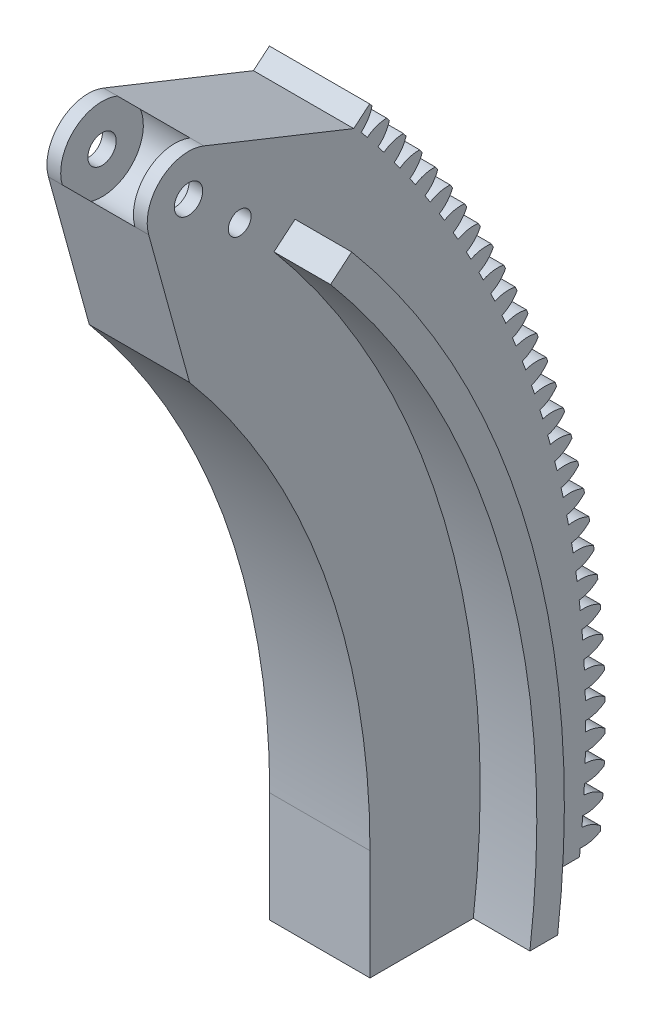
SolidWorks part; units mm, degrees
material "ABS"
ref_plane "Front Plane" through (0, 0, 0) normal (0, 0, 1) x (1, 0, 0)
ref_plane "Top Plane" through (0, 0, 0) normal (0, 1, 0) x (1, 0, 0)
ref_plane "Right Plane" through (0, 0, 0) normal (1, 0, 0) x (0, 0, -1)
ref_plane "idk" through (6.35, 0, 0) normal (1, 0, 0) x (0, 0, -1)
sketch "Sketch1" plane through (0, 0, 0) normal (1, 0, 0) x (0, 0, -1)
  line L0 (-1000, 0) -> (177.8, 0) construction
  line L1 (177.8, 0) -> (177.8, -25.4)
  line L2 (0, 0) -> (136.2027, 114.2876) construction
  line L4 (227.2, 0) -> (49000, 0) construction
  line L7 (177.8, -25.4) -> (227.2, -25.4) construction
  line L8 (227.2, 0) -> (227.2, -25.4) construction
  line L10 (-1.0719, -0.8495) -> (179.1555, 141.9904) construction
  line L61 (181.0098, 139.6187) -> (0, 0) construction
  line L62 (136.2027, 114.2876) -> (126.7844, 148.4774)
  line L64 (177.8, -25.4) -> (225.7757, -25.4)
  line L65 (136.2027, 114.2876) -> (155.124, 130.1645) construction
  line L66 (155.124, 130.1645) -> (174.0453, 146.0413) construction
  line L68 (0, 0) -> (35966.99, 34732.9185) construction
  line L69 (178.0587, 141.1212) -> (178.0836, 141.1409) construction
  line L70 (0, 0) -> (135.9673, 151.007) construction
  line L71 (139.5033, 159.8514) -> (174.0453, 146.0413)
  arc A2 (177.8, 0) -> (136.2027, 114.2876) centre (0, 0) ccw
  circle A19 centre (0, 0) radius 228.6 construction
  arc A22 (174.0453, 146.0413) -> (227.2, 0) centre (0, 0) cw
  arc A23 (227.2, 0) -> (225.7757, -25.4) centre (0, 0) cw
  arc A24 (126.7844, 148.4774) -> (139.5033, 159.8514) centre (135.9673, 151.007) cw
  point P6 (178.0836, 141.1409)
  point P7 (136.2027, 114.2876)
  dimension "D1" = 177.8
  dimension "D2" = 6.35
  dimension "D12" = 457.2
  dimension "D8" = 9.525
  dimension "D3" = 40
  dimension "D4" = 49.4
  dimension "D5" = 25.4
  dimension "D6" = 203.2
  dimension "D7" = 48
  dimension "D13" = 44
sketch "Sketch2" plane through (6.35, 0, 0) normal (1, 0, 0) x (0, 0, -1)
  line L0 (0, 0) -> (165.1, 0) construction
  line L1 (165.1, 0) -> (190.5, 0) construction
  line L2 (0, 0) -> (49240.3877, 8682.4089) construction
  circle A0 centre (165.1, 0) radius 3.2639
  circle A1 centre (190.5, 0) radius 3.2639
  arc A3 (165.1, 0) -> (162.5918, 28.6693) centre (0, 0) ccw construction
  circle A4 centre (162.5918, 28.6693) radius 3.2639
  arc A5 (190.5, 0) -> (187.6059, 33.08) centre (0, 0) ccw construction
  circle A6 centre (187.6059, 33.08) radius 3.2639
  dimension "D3" = 6.5278
  dimension "D4" = 6.5278
  dimension "D6" = 6.5278
  dimension "D7" = 6.5278
  dimension "D1" = 165.1
  dimension "D2" = 25.4
  dimension "D5" = 10
sketch "Sketch11" plane through (6.35, 0, 0) normal (1, 0, 0) x (0, 0, -1)
  line L0 (-785.502, -659.1144) -> (0, 0) construction
  line L2 (-1000, 0) -> (0, 0) construction
  line L4 (155.6602, 130.6144) -> (177.7223, 149.1267)
  line L5 (177.7223, 149.1267) -> (921.7047, 773.4021) construction
  line L6 (232, 0) -> (232, -25.4) construction
  line L7 (232, -25.4) -> (222.9391, -25.4) construction
  line L8 (201.6062, -25.4) -> (230.6054, -25.4)
  line L9 (203.2, 0) -> (232, 0) construction
  arc A0 (-230, 0) -> (-176.1902, -147.8412) centre (0, 0) ccw construction
  arc A1 (-232, 0) -> (-177.7223, -149.1267) centre (0, 0) ccw construction
  arc A2 (-229.6, 0) -> (-175.8838, -147.584) centre (0, 0) ccw construction
  arc A3 (232, 0) -> (177.7223, 149.1267) centre (0, 0) ccw
  arc A4 (230, 0) -> (176.1902, 147.8412) centre (0, 0) ccw construction
  arc A5 (-229.6, 0) -> (-175.8838, -147.584) centre (0, 0) ccw
  arc A6 (155.6602, 130.6144) -> (203.2, 0) centre (0, 0) cw
  arc A7 (232, 0) -> (230.6054, -25.4) centre (0, 0) cw
  arc A8 (203.2, 0) -> (201.6062, -25.4) centre (0, 0) cw
  dimension "D1" = 460
  dimension "D2" = 464
  dimension "D4" = 203.2
  dimension "D3" = 2.4
  dimension "D6" = 25.4
extrude "Teeth blank" add sketch "Sketch11" against normal blind 6.35
sketch "Sketch12" plane through (6.35, 0, 0) normal (1, 0, 0) x (0, 0, -1)
  line L0 (0, 0) -> (232, 0) construction
  line L2 (229.9946, 1.5708) -> (229.9946, -1.5708) construction
  line L3 (0, 0) -> (227.4972, 1.1241) construction
  line L4 (225.6789, 0) -> (232.9848, 2.6591) construction
  line L5 (0, 0) -> (232.9783, 3.1825) construction
  line L6 (229.9946, 1.5708) -> (229.9517, 4.7121) construction
  circle A0 centre (0, 0) radius 230 construction
  arc A1 (230.6054, -25.4) -> (177.7223, 149.1267) centre (0, 0) ccw construction
  circle A2 centre (0, 0) radius 227.5 construction
  arc A3 (227.4972, 1.1241) -> (232.9725, 3.5819) centre (227.4606, 8.5329) ccw
  arc A4 (231.5994, -25.5095) -> (232.9725, -3.5819) centre (0, 0) cw construction
  arc A5 (227.4972, -1.1241) -> (232.9725, -3.5819) centre (227.4606, -8.5329) cw
  arc A6 (231.5994, -25.5095) -> (178.4884, 149.7695) centre (0, 0) ccw
  arc A7 (231.5994, -25.5095) -> (232.9725, 3.5819) centre (0, 0) ccw construction
  arc A8 (227.4972, 1.1241) -> (227.4972, -1.1241) centre (0, 0) cw
  arc A9 (230.6054, -25.4) -> (177.7223, 149.1267) centre (0, 0) ccw construction
  arc A10 (232.9725, 3.5819) -> (232.9725, -3.5819) centre (0, 0) cw
  dimension "D1" = 460
  dimension "D3" = 20
  dimension "D4" = 0.783
  dimension "D5" = 4.5
  dimension "D2" = 1
extrude "Primary blank" add sketch "Sketch1" along normal blind 29.464
extrude "Tooth cut" cut sketch "Sketch12" against normal blind 6.35
pattern_circular "Tooth pattern" count 230 every 1.565 about axis through (0, 0, 0) along (1, 0, 0) of "Tooth cut"
sketch "Sketch15" plane through (6.35, 0, 0) normal (1, 0, 0) x (0, 0, -1)
  line L0 (0, 0) -> (135.9673, 151.007) construction
  line L2 (0, 0) -> (102.4673, 0) construction
  circle A0 centre (135.9673, 151.007) radius 3.2639
  dimension "D3" = 6.5278
  dimension "D1" = 203.2
  dimension "D2" = 48
extrude "Holes for top support" cut sketch "Sketch15" against normal through all both and the other way through all
sketch "Sketch22" plane through (6.35, 0, 0) normal (1, 0, 0) x (0, 0, -1)
  line L0 (0, 0) -> (135.9673, 151.007)
  line L1 (0, 0) -> (177.8, 0)
  dimension "D1" = 177.8
sketch "Sketch23" plane through (0, 0, 0) normal (1, 0, 0) x (0, 0, -1)
  line L0 (0, 0) -> (177.8, 0) construction
  line L1 (0, 0) -> (136.2027, 114.2876) construction
  line L2 (177.8, 0) -> (196.85, 0) construction
  line L3 (136.2027, 114.2876) -> (155.6602, 130.6144) construction
  line L5 (155.6602, 130.6144) -> (160.5246, 134.6961)
  line L7 (201.6062, -25.4) -> (0, 0) construction
  line L8 (208.0049, -25.4) -> (201.6062, -25.4)
  line L9 (177.8, -25.4) -> (226.0776, -25.4) construction
  arc A0 (177.8, 0) -> (136.2027, 114.2876) centre (0, 0) ccw construction
  circle A2 centre (196.85, 0) radius 6.35 construction
  arc A3 (203.2, 0) -> (155.6602, 130.6144) centre (0, 0) ccw
  arc A4 (209.55, 0) -> (160.5246, 134.6961) centre (0, 0) ccw
  circle A5 centre (215.9, 0) radius 6.35 construction
  arc A6 (203.2, 0) -> (201.6062, -25.4) centre (0, 0) cw
  arc A7 (209.55, 0) -> (208.0049, -25.4) centre (0, 0) cw
  dimension "D4" = 6.35
  dimension "D5" = 12.7
  dimension "D6" = 12.7
  dimension "D1" = 177.8
  dimension "D2" = 40
  dimension "D3" = 19.05
extrude "Thing to slide along bearings" add sketch "Sketch23" against normal blind 9.8742
ref_plane "Mirror plane" through (14.732, 0, 0) normal (1, 0, 0) x (0, 0, -1)
mirror "Mirroring slider" about plane through (14.732, 0, 0) normal (1, 0, 0) of "Thing to slide along bearings"
sketch "Sketch27" plane through (6.35, 0, 0) normal (1, 0, 0) x (0, 0, -1)
  line L2 (177.7223, 149.1267) -> (174.0453, 146.0413)
  line L3 (177.7223, 149.1267) -> (174.0453, 146.0413)
  line L7 (225.7757, -25.4) -> (226.0776, -25.4)
  line L8 (225.7757, -25.4) -> (226.0776, -25.4)
  arc A4 (227.2191, 11.3011) -> (227.0964, 13.5458) centre (0, 0) ccw
  arc A95 (231.8253, 9.0012) -> (231.7841, 10.0069) centre (0, 0) ccw
  arc A111 (227.3816, 7.3377) -> (231.8253, 9.0012) centre (227.1427, 14.7428) ccw
  arc A112 (227.3816, 7.3377) -> (231.8253, 9.0012) centre (227.1427, 14.7428) ccw
  arc A113 (231.7841, 10.0069) -> (227.2191, 11.3011) centre (227.5872, 3.9012) ccw
  arc A114 (231.7841, 10.0069) -> (227.2191, 11.3011) centre (227.5872, 3.9012) ccw
  arc A139 (227.2191, 11.3011) -> (227.0964, 13.5458) centre (0, 0) ccw
  arc A141 (227.0964, 13.5458) -> (231.493, 15.3301) centre (226.6552, 20.9417) ccw
  arc A143 (227.0964, 13.5458) -> (231.493, 15.3301) centre (226.6552, 20.9417) ccw
  arc A145 (231.493, 15.3301) -> (231.4243, 16.3343) centre (0, 0) ccw
  arc A147 (231.493, 15.3301) -> (231.4243, 16.3343) centre (0, 0) ccw
  arc A149 (231.4243, 16.3343) -> (226.8257, 17.5033) centre (227.3957, 10.1163) ccw
  arc A151 (231.4243, 16.3343) -> (226.8257, 17.5033) centre (227.3957, 10.1163) ccw
  arc A153 (226.8257, 17.5033) -> (226.6416, 19.7439) centre (0, 0) ccw
  arc A155 (226.8257, 17.5033) -> (226.6416, 19.7439) centre (0, 0) ccw
  arc A157 (226.6416, 19.7439) -> (230.9878, 21.6476) centre (225.9986, 27.1249) ccw
  arc A159 (226.6416, 19.7439) -> (230.9878, 21.6476) centre (225.9986, 27.1249) ccw
  arc A161 (230.9878, 21.6476) -> (230.8918, 22.6495) centre (0, 0) ccw
  arc A163 (230.9878, 21.6476) -> (230.8918, 22.6495) centre (0, 0) ccw
  arc A165 (230.8918, 22.6495) -> (226.2629, 23.6925) centre (227.0345, 16.3238) ccw
  arc A167 (230.8918, 22.6495) -> (226.2629, 23.6925) centre (227.0345, 16.3238) ccw
  arc A169 (226.2629, 23.6925) -> (226.0178, 25.9272) centre (0, 0) ccw
  arc A171 (226.2629, 23.6925) -> (226.0178, 25.9272) centre (0, 0) ccw
  arc A173 (226.0178, 25.9272) -> (230.3104, 27.9489) centre (225.1734, 33.2879) ccw
  arc A175 (226.0178, 25.9272) -> (230.3104, 27.9489) centre (225.1734, 33.2879) ccw
  arc A177 (230.3104, 27.9489) -> (230.1869, 28.9478) centre (0, 0) ccw
  arc A179 (230.3104, 27.9489) -> (230.1869, 28.9478) centre (0, 0) ccw
  arc A181 (230.1869, 28.9478) -> (225.5314, 29.8639) centre (226.5039, 22.5191) ccw
  arc A182 (230.1869, 28.9478) -> (225.5314, 29.8639) centre (226.5039, 22.5191) ccw
  arc A184 (225.5314, 29.8639) -> (225.2252, 32.0911) centre (0, 0) ccw
  arc A186 (225.5314, 29.8639) -> (225.2252, 32.0911) centre (0, 0) ccw
  arc A189 (231.8253, 9.0012) -> (231.7841, 10.0069) centre (0, 0) ccw
  arc A282 (225.2252, 32.0911) -> (229.461, 34.2294) centre (224.1801, 39.426) ccw
  arc A284 (225.2252, 32.0911) -> (229.461, 34.2294) centre (224.1801, 39.426) ccw
  arc A286 (229.461, 34.2294) -> (229.3104, 35.2245) centre (0, 0) ccw
  arc A288 (229.461, 34.2294) -> (229.3104, 35.2245) centre (0, 0) ccw
  arc A290 (229.3104, 35.2245) -> (224.6315, 36.0131) centre (225.8043, 28.6976) ccw
  arc A292 (229.3104, 35.2245) -> (224.6315, 36.0131) centre (225.8043, 28.6976) ccw
  arc A294 (224.6315, 36.0131) -> (224.2647, 38.2311) centre (0, 0) ccw
  arc A296 (224.6315, 36.0131) -> (224.2647, 38.2311) centre (0, 0) ccw
  arc A298 (224.2647, 38.2311) -> (228.4404, 40.4843) centre (223.0196, 45.5347) ccw
  arc A300 (224.2647, 38.2311) -> (228.4404, 40.4843) centre (223.0196, 45.5347) ccw
  arc A302 (228.4404, 40.4843) -> (228.2626, 41.4749) centre (0, 0) ccw
  arc A304 (228.4404, 40.4843) -> (228.2626, 41.4749) centre (0, 0) ccw
  arc A306 (228.2626, 41.4749) -> (223.564, 42.1355) centre (224.9362, 34.8547) ccw
  arc A308 (228.2626, 41.4749) -> (223.564, 42.1355) centre (224.9362, 34.8547) ccw
  arc A310 (223.564, 42.1355) -> (223.1367, 44.3426) centre (0, 0) ccw
  arc A312 (223.564, 42.1355) -> (223.1367, 44.3426) centre (0, 0) ccw
  arc A314 (223.1367, 44.3426) -> (227.2494, 46.709) centre (221.6926, 51.6095) ccw
  arc A316 (223.1367, 44.3426) -> (227.2494, 46.709) centre (221.6926, 51.6095) ccw
  arc A318 (227.2494, 46.709) -> (227.0446, 47.6944) centre (0, 0) ccw
  arc A320 (227.2494, 46.709) -> (227.0446, 47.6944) centre (0, 0) ccw
  arc A322 (227.0446, 47.6944) -> (222.3296, 48.2264) centre (223.9002, 40.9858) ccw
  arc A324 (227.0446, 47.6944) -> (222.3296, 48.2264) centre (223.9002, 40.9858) ccw
  arc A326 (222.3296, 48.2264) -> (221.8422, 50.421) centre (0, 0) ccw
  arc A328 (222.3296, 48.2264) -> (221.8422, 50.421) centre (0, 0) ccw
  arc A330 (221.8422, 50.421) -> (225.8887, 52.8988) centre (220.2002, 57.6457) ccw
  arc A332 (221.8422, 50.421) -> (225.8887, 52.8988) centre (220.2002, 57.6457) ccw
  arc A334 (225.8887, 52.8988) -> (225.6571, 53.8783) centre (0, 0) ccw
  arc A336 (225.8887, 52.8988) -> (225.6571, 53.8783) centre (0, 0) ccw
  arc A338 (225.6571, 53.8783) -> (220.9294, 54.2813) centre (222.6972, 47.0863) ccw
  arc A340 (225.6571, 53.8783) -> (220.9294, 54.2813) centre (222.6972, 47.0863) ccw
  arc A342 (220.9294, 54.2813) -> (220.3822, 56.4618) centre (0, 0) ccw
  arc A344 (220.9294, 54.2813) -> (220.3822, 56.4618) centre (0, 0) ccw
  arc A346 (220.3822, 56.4618) -> (224.3595, 59.0492) centre (218.5434, 63.6389) ccw
  arc A348 (220.3822, 56.4618) -> (224.3595, 59.0492) centre (218.5434, 63.6389) ccw
  arc A350 (224.3595, 59.0492) -> (224.1012, 60.022) centre (0, 0) ccw
  arc A352 (224.3595, 59.0492) -> (224.1012, 60.022) centre (0, 0) ccw
  arc A354 (224.1012, 60.022) -> (219.3643, 60.2956) centre (221.3279, 53.1516) ccw
  arc A356 (224.1012, 60.022) -> (219.3643, 60.2956) centre (221.3279, 53.1516) ccw
  arc A358 (219.3643, 60.2956) -> (218.7577, 62.4604) centre (0, 0) ccw
  arc A360 (219.3643, 60.2956) -> (218.7577, 62.4604) centre (0, 0) ccw
  arc A362 (218.7577, 62.4604) -> (222.6629, 65.1555) centre (216.7236, 69.5847) ccw
  arc A364 (218.7577, 62.4604) -> (222.6629, 65.1555) centre (216.7236, 69.5847) ccw
  arc A366 (222.6629, 65.1555) -> (222.3781, 66.1209) centre (0, 0) ccw
  arc A368 (222.6629, 65.1555) -> (222.3781, 66.1209) centre (0, 0) ccw
  arc A370 (222.3781, 66.1209) -> (217.6355, 66.265) centre (219.7935, 59.1773) ccw
  arc A372 (222.3781, 66.1209) -> (217.6355, 66.265) centre (219.7935, 59.1773) ccw
  arc A374 (217.6355, 66.265) -> (216.97, 68.4124) centre (0, 0) ccw
  arc A376 (217.6355, 66.265) -> (216.97, 68.4124) centre (0, 0) ccw
  arc A378 (216.97, 68.4124) -> (220.8001, 71.2132) centre (214.742, 75.4785) ccw
  arc A380 (216.97, 68.4124) -> (220.8001, 71.2132) centre (214.742, 75.4785) ccw
  arc A382 (220.8001, 71.2132) -> (220.4891, 72.1704) centre (0, 0) ccw
  arc A384 (220.8001, 71.2132) -> (220.4891, 72.1704) centre (0, 0) ccw
  arc A386 (220.4891, 72.1704) -> (215.7443, 72.185) centre (218.0951, 65.1589) ccw
  arc A388 (220.4891, 72.1704) -> (215.7443, 72.185) centre (218.0951, 65.1589) ccw
  arc A390 (215.7443, 72.185) -> (215.0204, 74.3134) centre (0, 0) ccw
  arc A394 (215.7443, 72.185) -> (215.0204, 74.3134) centre (0, 0) ccw
  arc A398 (215.0204, 74.3134) -> (218.7726, 77.2177) centre (212.6002, 81.3159) ccw
  arc A402 (215.0204, 74.3134) -> (218.7726, 77.2177) centre (212.6002, 81.3159) ccw
  arc A406 (218.7726, 77.2177) -> (218.4355, 78.1661) centre (0, 0) ccw
  arc A410 (218.7726, 77.2177) -> (218.4355, 78.1661) centre (0, 0) ccw
  arc A414 (218.4355, 78.1661) -> (213.692, 78.0511) centre (216.2339, 71.0918) ccw
  arc A418 (218.4355, 78.1661) -> (213.692, 78.0511) centre (216.2339, 71.0918) ccw
  arc A420 (213.692, 78.0511) -> (212.9103, 80.1589) centre (0, 0) ccw
  arc A422 (213.692, 78.0511) -> (212.9103, 80.1589) centre (0, 0) ccw
  arc A423 (212.9103, 80.1589) -> (216.5817, 83.1646) centre (210.2998, 87.0927) ccw
  arc A424 (212.9103, 80.1589) -> (216.5817, 83.1646) centre (210.2998, 87.0927) ccw
  arc A425 (216.5817, 83.1646) -> (216.2189, 84.1034) centre (0, 0) ccw
  arc A426 (216.5817, 83.1646) -> (216.2189, 84.1034) centre (0, 0) ccw
  arc A427 (216.2189, 84.1034) -> (211.4804, 83.8589) centre (214.2114, 76.9716) ccw
  arc A428 (216.2189, 84.1034) -> (211.4804, 83.8589) centre (214.2114, 76.9716) ccw
  arc A429 (211.4804, 83.8589) -> (210.6414, 85.9446) centre (0, 0) ccw
  arc A430 (211.4804, 83.8589) -> (210.6414, 85.9446) centre (0, 0) ccw
  arc A431 (210.6414, 85.9446) -> (214.2293, 89.0495) centre (207.8424, 92.8045) ccw
  arc A432 (210.6414, 85.9446) -> (214.2293, 89.0495) centre (207.8424, 92.8045) ccw
  arc A434 (214.2293, 89.0495) -> (213.841, 89.978) centre (0, 0) ccw
  arc A436 (214.2293, 89.0495) -> (213.841, 89.978) centre (0, 0) ccw
  arc A438 (213.841, 89.978) -> (209.1109, 89.6041) centre (212.029, 82.794) ccw
  arc A440 (213.841, 89.978) -> (209.1109, 89.6041) centre (212.029, 82.794) ccw
  arc A442 (209.1109, 89.6041) -> (208.2152, 91.6661) centre (0, 0) ccw
  arc A444 (209.1109, 89.6041) -> (208.2152, 91.6661) centre (0, 0) ccw
  arc A446 (208.2152, 91.6661) -> (211.717, 94.8679) centre (205.2299, 98.4471) ccw
  arc A448 (208.2152, 91.6661) -> (211.717, 94.8679) centre (205.2299, 98.4471) ccw
  arc A450 (211.717, 94.8679) -> (211.3034, 95.7855) centre (0, 0) ccw
  arc A452 (211.717, 94.8679) -> (211.3034, 95.7855) centre (0, 0) ccw
  arc A454 (211.3034, 95.7855) -> (206.5853, 95.2825) centre (209.6884, 88.5547) ccw
  arc A456 (211.3034, 95.7855) -> (206.5853, 95.2825) centre (209.6884, 88.5547) ccw
  arc A458 (206.5853, 95.2825) -> (205.6337, 97.3193) centre (0, 0) ccw
  arc A460 (206.5853, 95.2825) -> (205.6337, 97.3193) centre (0, 0) ccw
  arc A462 (205.6337, 97.3193) -> (209.0467, 100.6155) centre (202.4643, 104.0162) ccw
  arc A464 (205.6337, 97.3193) -> (209.0467, 100.6155) centre (202.4643, 104.0162) ccw
  arc A466 (209.0467, 100.6155) -> (208.6082, 101.5215) centre (0, 0) ccw
  arc A467 (209.0467, 100.6155) -> (208.6082, 101.5215) centre (0, 0) ccw
  arc A468 (208.6082, 101.5215) -> (203.9056, 100.8898) centre (207.1913, 94.2492) ccw
  arc A469 (208.6082, 101.5215) -> (203.9056, 100.8898) centre (207.1913, 94.2492) ccw
  arc A470 (203.9056, 100.8898) -> (202.8987, 102.8998) centre (0, 0) ccw
  arc A471 (203.9056, 100.8898) -> (202.8987, 102.8998) centre (0, 0) ccw
  arc A472 (202.8987, 102.8998) -> (206.2204, 106.288) centre (199.5476, 109.5076) ccw
  arc A473 (202.8987, 102.8998) -> (206.2204, 106.288) centre (199.5476, 109.5076) ccw
  arc A474 (206.2204, 106.288) -> (205.7574, 107.1817) centre (0, 0) ccw
  arc A475 (206.2204, 106.288) -> (205.7574, 107.1817) centre (0, 0) ccw
  arc A476 (205.7574, 107.1817) -> (201.0737, 106.4218) centre (204.5396, 99.8735) ccw
  arc A477 (205.7574, 107.1817) -> (201.0737, 106.4218) centre (204.5396, 99.8735) ccw
  arc A478 (201.0737, 106.4218) -> (200.0123, 108.4036) centre (0, 0) ccw
  arc A479 (201.0737, 106.4218) -> (200.0123, 108.4036) centre (0, 0) ccw
  arc A480 (200.0123, 108.4036) -> (203.2402, 111.8812) centre (196.4819, 114.9174) ccw
  arc A481 (200.0123, 108.4036) -> (203.2402, 111.8812) centre (196.4819, 114.9174) ccw
  arc A482 (203.2402, 111.8812) -> (202.7529, 112.7619) centre (0, 0) ccw
  arc A483 (203.2402, 111.8812) -> (202.7529, 112.7619) centre (0, 0) ccw
  arc A484 (202.7529, 112.7619) -> (198.0918, 111.8744) centre (201.7352, 105.4232) ccw
  arc A485 (202.7529, 112.7619) -> (198.0918, 111.8744) centre (201.7352, 105.4232) ccw
  arc A486 (198.0918, 111.8744) -> (196.9766, 113.8264) centre (0, 0) ccw
  arc A487 (198.0918, 111.8744) -> (196.9766, 113.8264) centre (0, 0) ccw
  arc A488 (196.9766, 113.8264) -> (200.1084, 117.3909) centre (193.2697, 120.2413) ccw
  arc A489 (196.9766, 113.8264) -> (200.1084, 117.3909) centre (193.2697, 120.2413) ccw
  arc A490 (200.1084, 117.3909) -> (199.5972, 118.258) centre (0, 0) ccw
  arc A491 (200.1084, 117.3909) -> (199.5972, 118.258) centre (0, 0) ccw
  arc A492 (199.5972, 118.258) -> (194.9621, 117.2435) centre (198.7804, 110.8942) ccw
  arc A493 (199.5972, 118.258) -> (194.9621, 117.2435) centre (198.7804, 110.8942) ccw
  arc A494 (194.9621, 117.2435) -> (193.794, 119.1643) centre (0, 0) ccw
  arc A495 (194.9621, 117.2435) -> (193.794, 119.1643) centre (0, 0) ccw
  arc A496 (193.794, 119.1643) -> (196.8272, 122.8131) centre (189.9132, 125.4756) ccw
  arc A497 (193.794, 119.1643) -> (196.8272, 122.8131) centre (189.9132, 125.4756) ccw
  arc A498 (196.8272, 122.8131) -> (196.2926, 123.6658) centre (0, 0) ccw
  arc A499 (196.8272, 122.8131) -> (196.2926, 123.6658) centre (0, 0) ccw
  arc A500 (196.2926, 123.6658) -> (191.6869, 122.5251) centre (195.6771, 116.2824) ccw
  arc A501 (196.2926, 123.6658) -> (191.6869, 122.5251) centre (195.6771, 116.2824) ccw
  arc A502 (191.6869, 122.5251) -> (190.4667, 124.4133) centre (0, 0) ccw
  arc A503 (191.6869, 122.5251) -> (190.4667, 124.4133) centre (0, 0) ccw
  arc A504 (190.4667, 124.4133) -> (193.3992, 128.1435) centre (186.415, 130.6162) ccw
  arc A505 (190.4667, 124.4133) -> (193.3992, 128.1435) centre (186.415, 130.6162) ccw
  arc A506 (193.3992, 128.1435) -> (192.8414, 128.9814) centre (0, 0) ccw
  arc A507 (193.3992, 128.1435) -> (192.8414, 128.9814) centre (0, 0) ccw
  arc A508 (192.8414, 128.9814) -> (188.2686, 127.7153) centre (192.4279, 121.5839) ccw
  arc A509 (192.8414, 128.9814) -> (188.2686, 127.7153) centre (192.4279, 121.5839) ccw
  arc A510 (188.2686, 127.7153) -> (186.9974, 129.5694) centre (0, 0) ccw
  arc A511 (188.2686, 127.7153) -> (186.9974, 129.5694) centre (0, 0) ccw
  arc A512 (186.9974, 129.5694) -> (189.8268, 133.3784) centre (182.7777, 135.6594) ccw
  arc A513 (186.9974, 129.5694) -> (189.8268, 133.3784) centre (182.7777, 135.6594) ccw
  arc A514 (189.8268, 133.3784) -> (189.2464, 134.2007) centre (0, 0) ccw
  arc A515 (189.8268, 133.3784) -> (189.2464, 134.2007) centre (0, 0) ccw
  arc A516 (189.2464, 134.2007) -> (184.7098, 132.8101) centre (189.0351, 126.7947) ccw
  arc A517 (189.2464, 134.2007) -> (184.7098, 132.8101) centre (189.0351, 126.7947) ccw
  arc A518 (184.7098, 132.8101) -> (183.3884, 134.6289) centre (0, 0) ccw
  arc A519 (184.7098, 132.8101) -> (183.3884, 134.6289) centre (0, 0) ccw
  arc A520 (225.7757, -25.4) -> (174.0453, 146.0413) centre (0, 0) ccw
  arc A521 (225.7757, -25.4) -> (174.0453, 146.0413) centre (0, 0) ccw
  arc A522 (227.4972, -1.1241) -> (227.4972, 1.1241) centre (0, 0) ccw
  arc A523 (227.4972, -1.1241) -> (227.4972, 1.1241) centre (0, 0) ccw
  arc A524 (227.4972, 1.1241) -> (231.9847, 2.6656) centre (227.4606, 8.5329) ccw
  arc A525 (227.4972, 1.1241) -> (231.9847, 2.6656) centre (227.4606, 8.5329) ccw
  arc A526 (231.9847, 2.6656) -> (231.9709, 3.672) centre (0, 0) ccw
  arc A527 (231.9847, 2.6656) -> (231.9709, 3.672) centre (0, 0) ccw
  arc A528 (231.9709, 3.672) -> (227.4431, 5.0904) centre (227.6088, -2.3167) ccw
  arc A529 (231.9709, 3.672) -> (227.4431, 5.0904) centre (227.6088, -2.3167) ccw
  arc A530 (227.4431, 5.0904) -> (227.3816, 7.3377) centre (0, 0) ccw
  arc A531 (227.4431, 5.0904) -> (227.3816, 7.3377) centre (0, 0) ccw
  arc A532 (231.9709, -3.672) -> (231.9847, -2.6656) centre (0, 0) ccw
  arc A533 (231.9709, -3.672) -> (231.9847, -2.6656) centre (0, 0) ccw
  arc A534 (231.9847, -2.6656) -> (227.4972, -1.1241) centre (227.4606, -8.5329) ccw
  arc A535 (231.9847, -2.6656) -> (227.4972, -1.1241) centre (227.4606, -8.5329) ccw
  arc A536 (183.3884, 134.6289) -> (186.1128, 138.5137) centre (179.004, 140.6013) ccw
  arc A537 (183.3884, 134.6289) -> (186.1128, 138.5137) centre (179.004, 140.6013) ccw
  arc A538 (186.1128, 138.5137) -> (185.5101, 139.3198) centre (0, 0) ccw
  arc A539 (186.1128, 138.5137) -> (185.5101, 139.3198) centre (0, 0) ccw
  arc A540 (185.5101, 139.3198) -> (181.0132, 137.8059) centre (185.5011, 131.9108) ccw
  arc A541 (185.5101, 139.3198) -> (181.0132, 137.8059) centre (185.5011, 131.9108) ccw
  arc A542 (181.0132, 137.8059) -> (179.6426, 139.5879) centre (0, 0) ccw
  arc A543 (181.0132, 137.8059) -> (179.6426, 139.5879) centre (0, 0) ccw
  arc A544 (179.6426, 139.5879) -> (182.2598, 143.5456) centre (175.0967, 145.4383) ccw
  arc A545 (179.6426, 139.5879) -> (182.2598, 143.5456) centre (175.0967, 145.4383) ccw
  arc A546 (182.2598, 143.5456) -> (181.6354, 144.335) centre (0, 0) ccw
  arc A547 (182.2598, 143.5456) -> (181.6354, 144.335) centre (0, 0) ccw
  arc A548 (181.6354, 144.335) -> (177.1815, 142.6988) centre (181.8288, 136.9286) ccw
  arc A549 (181.6354, 144.335) -> (177.1815, 142.6988) centre (181.8288, 136.9286) ccw
  arc A550 (177.1815, 142.6988) -> (175.7628, 144.4427) centre (0, 0) ccw
  arc A551 (177.1815, 142.6988) -> (175.7628, 144.4427) centre (0, 0) ccw
  arc A552 (175.7628, 144.4427) -> (178.2709, 148.4705) centre (171.0587, 150.1668) ccw
  arc A553 (175.7628, 144.4427) -> (178.2709, 148.4705) centre (171.0587, 150.1668) ccw
  arc A554 (178.2709, 148.4705) -> (177.7223, 149.1267) centre (0, 0) ccw
  arc A555 (178.2709, 148.4705) -> (177.7223, 149.1267) centre (0, 0) ccw
  arc A556 (226.0776, -25.4) -> (226.2629, -23.6925) centre (0, 0) ccw
  arc A557 (226.0776, -25.4) -> (226.2629, -23.6925) centre (0, 0) ccw
  arc A558 (226.2629, -23.6925) -> (230.8918, -22.6495) centre (227.0345, -16.3238) ccw
  arc A559 (226.2629, -23.6925) -> (230.8918, -22.6495) centre (227.0345, -16.3238) ccw
  arc A560 (230.8918, -22.6495) -> (230.9878, -21.6476) centre (0, 0) ccw
  arc A561 (230.8918, -22.6495) -> (230.9878, -21.6476) centre (0, 0) ccw
  arc A562 (230.9878, -21.6476) -> (226.6416, -19.7439) centre (225.9986, -27.1249) ccw
  arc A563 (230.9878, -21.6476) -> (226.6416, -19.7439) centre (225.9986, -27.1249) ccw
  arc A564 (226.6416, -19.7439) -> (226.8257, -17.5033) centre (0, 0) ccw
  arc A565 (226.6416, -19.7439) -> (226.8257, -17.5033) centre (0, 0) ccw
  arc A566 (226.8257, -17.5033) -> (231.4243, -16.3343) centre (227.3957, -10.1163) ccw
  arc A567 (226.8257, -17.5033) -> (231.4243, -16.3343) centre (227.3957, -10.1163) ccw
  arc A568 (231.4243, -16.3343) -> (231.493, -15.3301) centre (0, 0) ccw
  arc A569 (231.4243, -16.3343) -> (231.493, -15.3301) centre (0, 0) ccw
  arc A570 (231.493, -15.3301) -> (227.0964, -13.5458) centre (226.6552, -20.9417) ccw
  arc A571 (231.493, -15.3301) -> (227.0964, -13.5458) centre (226.6552, -20.9417) ccw
  arc A572 (227.0964, -13.5458) -> (227.2191, -11.3011) centre (0, 0) ccw
  arc A573 (227.0964, -13.5458) -> (227.2191, -11.3011) centre (0, 0) ccw
  arc A574 (227.2191, -11.3011) -> (231.7841, -10.0069) centre (227.5872, -3.9012) ccw
  arc A575 (227.2191, -11.3011) -> (231.7841, -10.0069) centre (227.5872, -3.9012) ccw
  arc A576 (231.7841, -10.0069) -> (231.8253, -9.0012) centre (0, 0) ccw
  arc A577 (231.7841, -10.0069) -> (231.8253, -9.0012) centre (0, 0) ccw
  arc A578 (231.8253, -9.0012) -> (227.3816, -7.3377) centre (227.1427, -14.7428) ccw
  arc A579 (231.8253, -9.0012) -> (227.3816, -7.3377) centre (227.1427, -14.7428) ccw
  arc A580 (227.3816, -7.3377) -> (227.4431, -5.0904) centre (0, 0) ccw
  arc A581 (227.3816, -7.3377) -> (227.4431, -5.0904) centre (0, 0) ccw
  arc A582 (227.4431, -5.0904) -> (231.9709, -3.672) centre (227.6088, 2.3167) ccw
  arc A583 (227.4431, -5.0904) -> (231.9709, -3.672) centre (227.6088, 2.3167) ccw
  dimension "D1" = 0
extrude "Extending teeth" add sketch "Sketch27" along normal blind 23.0187
ref_plane "Plane for cut for space for top support screws" through (6.35, 0, 0) normal (-1, 0, 0) x (0, 0, 1)
sketch "Sketch28" plane through (6.35, 0, 0) normal (1, 0, 0) x (0, 0, -1)
  circle A0 centre (135.9673, 151.007) radius 9.525
  arc A1 (139.5033, 159.8514) -> (126.7844, 148.4774) centre (135.9673, 151.007) ccw construction
extrude "Cut for space for top support screws" cut sketch "Sketch28" along normal blind 16.764
sketch "Sketch29" plane through (0, -25.4, 0) normal (0, -1, 0) x (1, 0, 0)
  line L0 (14.6844, -226.0776) -> (14.732, -177.8) construction
  line L1 (29.3687, -226.0776) -> (0, -226.0776) construction
  line L2 (29.464, -177.8) -> (0, -177.8) construction
  circle A0 centre (14.7082, -201.9388) radius 3.81
  dimension "D1" = 7.62
extrude "Holes for limit switch" cut sketch "Sketch29" against normal blind 12.7
sketch "Sketch30" plane through (29.464, 0, 0) normal (1, 0, 0) x (0, 0, -1)
  line L0 (174.0453, 146.0413) -> (183.7741, 154.2047)
  line L1 (225.7757, -25.4) -> (238.5516, -25.4)
  line L6 (155.6602, 130.6144) -> (160.5246, 134.6961)
  line L7 (208.0049, -25.4) -> (225.7757, -25.4)
  line L8 (174.0453, 146.0413) -> (139.5033, 159.8514)
  line L9 (126.7844, 148.4774) -> (136.2027, 114.2876)
  line L10 (177.8, 0) -> (177.8, -25.4)
  line L11 (177.8, -25.4) -> (201.6062, -25.4)
  line L12 (155.6602, 130.6144) -> (160.5246, 134.6961)
  line L13 (208.0049, -25.4) -> (225.7757, -25.4)
  line L14 (174.0453, 146.0413) -> (139.5033, 159.8514)
  line L15 (126.7844, 148.4774) -> (136.2027, 114.2876)
  line L16 (177.8, 0) -> (177.8, -25.4)
  line L17 (177.8, -25.4) -> (201.6062, -25.4)
  arc A0 (183.7741, 154.2047) -> (238.5516, -25.4) centre (0, 0) cw
  arc A5 (201.6062, -25.4) -> (155.6602, 130.6144) centre (0, 0) ccw
  arc A6 (208.0049, -25.4) -> (160.5246, 134.6961) centre (0, 0) ccw
  arc A7 (225.7757, -25.4) -> (174.0453, 146.0413) centre (0, 0) ccw
  arc A8 (139.5033, 159.8514) -> (126.7844, 148.4774) centre (135.9673, 151.007) ccw
  arc A9 (177.8, 0) -> (136.2027, 114.2876) centre (0, 0) ccw
  arc A10 (201.6062, -25.4) -> (155.6602, 130.6144) centre (0, 0) ccw
  arc A11 (208.0049, -25.4) -> (160.5246, 134.6961) centre (0, 0) ccw
  arc A12 (225.7757, -25.4) -> (174.0453, 146.0413) centre (0, 0) ccw construction
  arc A13 (139.5033, 159.8514) -> (126.7844, 148.4774) centre (135.9673, 151.007) ccw
  arc A14 (177.8, 0) -> (136.2027, 114.2876) centre (0, 0) ccw
  dimension "D2" = 12.7
  dimension "D1" = 0
extrude "Cut to make space for aluminum reinforcement plate" cut sketch "Sketch30" against normal blind 3.175
mirror "Mirroring the above cut" about plane through (14.732, 0, 0) normal (1, 0, 0) of "Cut to make space for aluminum reinforcement plate"
sketch "Sketch31" plane through (3.175, 0, 0) normal (-1, 0, 0) x (0, 0, 1)
  line L0 (-135.9673, 151.007) -> (-147.7648, 140.3846) construction
  line L1 (-135.9673, 151.007) -> (0, 0) construction
  circle A0 centre (-147.7648, 140.3846) radius 2.6289
  dimension "D2" = 5.2578
  dimension "D1" = 15.875
extrude "Hole for additional bolt for reinforcement plate" cut sketch "Sketch31" against normal through all
sketch "Sketch32" plane through (0, -25.4, 0) normal (0, -1, 0) x (1, 0, 0)
  line L0 (14.7082, -201.9388) -> (14.7082, -214.6388) construction
  line L1 (14.7082, -201.9388) -> (12.9916, -201.9388) construction
  circle A0 centre (14.7082, -214.6388) radius 4.7625
  circle A1 centre (14.7082, -189.2388) radius 4.7625
  dimension "D2" = 9.525
  dimension "D1" = 12.7
extrude "Cut-Extrude1" cut sketch "Sketch32" against normal blind 1.27
equation "\"Module\"= 2mm"
equation "\"Number of Teeth\"= 230"
equation "\"D1@Sketch12\"=\"Module\" * \"Number of Teeth\""
equation "\"D4@Sketch12\"=180 / \"Number of Teeth\""
equation "\"D2\"= 360 / \"Number of Teeth\""
equation "\"D2@Sketch11\"=( \"Number of Teeth\" + 2) * \"Module\""
equation "\"D2@Tooth pattern\" = 360 / \"Number of Teeth\""
equation "\"D5@Sketch12\"= 2.25 * \"Module\""
equation "\"D1@Tooth pattern\" = \"Number of Teeth\""
